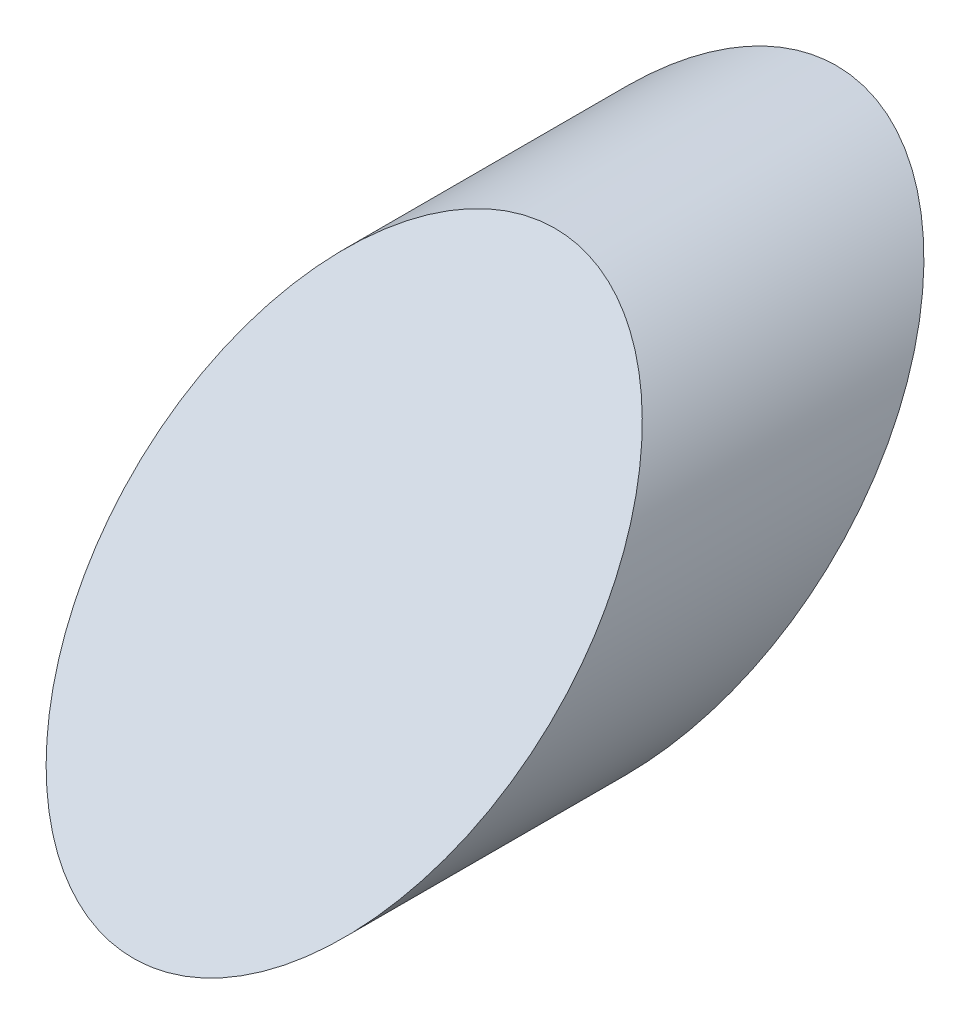
SolidWorks part; units mm, degrees
material "Glass"
ref_plane "Front Plane" through (0, 0, 0) normal (0, 0, 1) x (1, 0, 0)
ref_plane "Top Plane" through (0, 0, 0) normal (0, 1, 0) x (1, 0, 0)
ref_plane "Right Plane" through (0, 0, 0) normal (1, 0, 0) x (0, 0, -1)
sketch "Sketch1" plane through (0, 0, 0) normal (0, 0, 1) x (1, 0, 0)
  circle A0 centre (0, 0) radius 6.35
  dimension "D1" = 12.7
extrude "Boss-Extrude1" add sketch "Sketch1" along normal blind 25.4
sketch "Sketch3" plane through (0, 0, 0) normal (1, 0, 0) x (0, 0, -1)
  line L0 (-25.6175, -10.7822) -> (-2.9129, 11.9224)
  line L1 (-2.9129, 11.9224) -> (5.5724, 11.9224)
  line L2 (5.5724, 11.9224) -> (-17.1322, -10.7822)
  line L3 (-17.1322, -10.7822) -> (-25.6175, -10.7822)
  line L4 (-25.4, -6.35) -> (0, -6.35) construction
  point P6 (0, 6.35)
  point P10 (0, 0)
  dimension "D1" = 45
  dimension "D2" = 6
extrude "Cut-Extrude1" cut sketch "Sketch3" against normal through all both and the other way through all flip side to cut
sketch "Sketch4" plane through (0, 0, 0) normal (1, 0, 0) x (0, 0, -1)
  line L0 (-1000, 0) -> (49000, 0) construction
  line L1 (-8.4853, 6.35) -> (-21.1853, -6.35) construction
  line L2 (-96.0014, 0) -> (-8.4853, 6.35) construction
  line L3 (-96.0014, 0) -> (-20.3261, -5.4909) construction
  line L4 (-8.4853, 6.35) -> (-5.5124, 47.3231) construction
  line L5 (-20.3261, -5.4909) -> (-24.1582, 47.3231) construction
  line L6 (-14.8353, 0) -> (-14.8353, 47.3231) construction
  point P1 (-14.8353, 0)
  point P15 (-14.8353, 39.8303)
  point P17 (-14.8353, 47.3231)
  dimension "D1" = 4.15
  dimension "D2" = 4.15
  dimension "D3" = 4.15
  dimension "D4" = 4.15
equation "\"D2@Sketch4\"=\"D1@Sketch4\""
equation "\"D3@Sketch4\"=\"D2@Sketch4\""
equation "\"D4@Sketch4\"=\"D2@Sketch4\""
